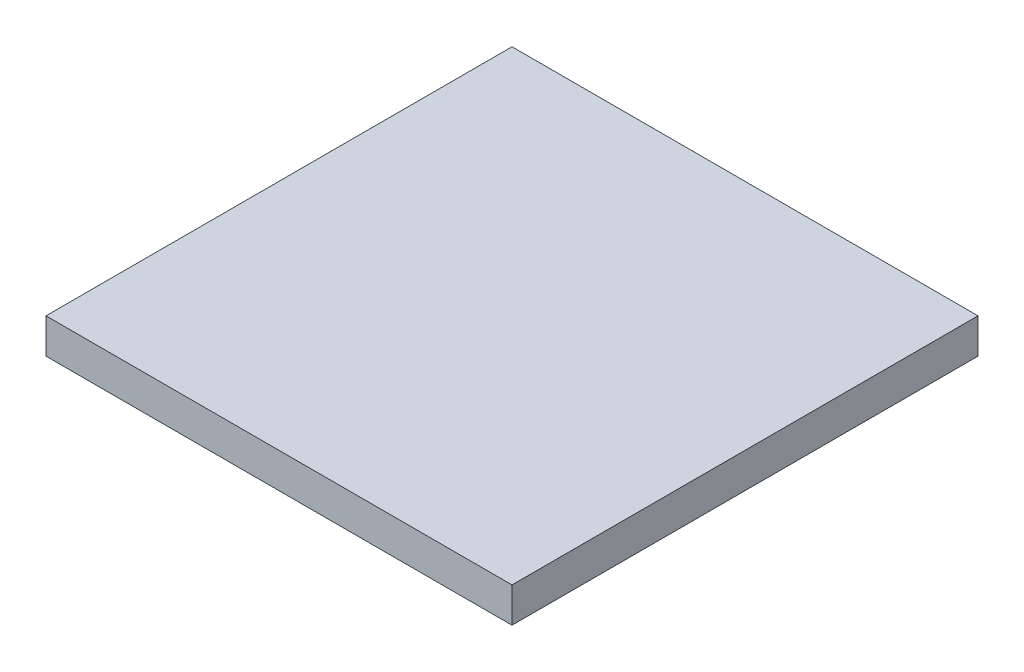
SolidWorks part; units mm, degrees
ref_plane "Спереди" through (0, 0, 0) normal (0, 0, 1) x (1, 0, 0)
ref_plane "Сверху" through (0, 0, 0) normal (0, 1, 0) x (1, 0, 0)
ref_plane "Справа" through (0, 0, 0) normal (1, 0, 0) x (0, 0, -1)
sketch "Эскиз1" plane through (0, 0, 0) normal (0, 1, 0) x (1, 0, 0)
  line L1 (-8.3803, 15) -> (11.6197, 15)
  line L2 (-8.3803, 15) -> (-8.3803, -5)
  line L3 (-8.3803, -5) -> (11.6197, -5)
  line L4 (11.6197, 15) -> (11.6197, -5)
  dimension "D1" = 20
  dimension "D2" = 20
extrude "Бобышка-Вытянуть1" add sketch "Эскиз1" along normal blind 1.5
